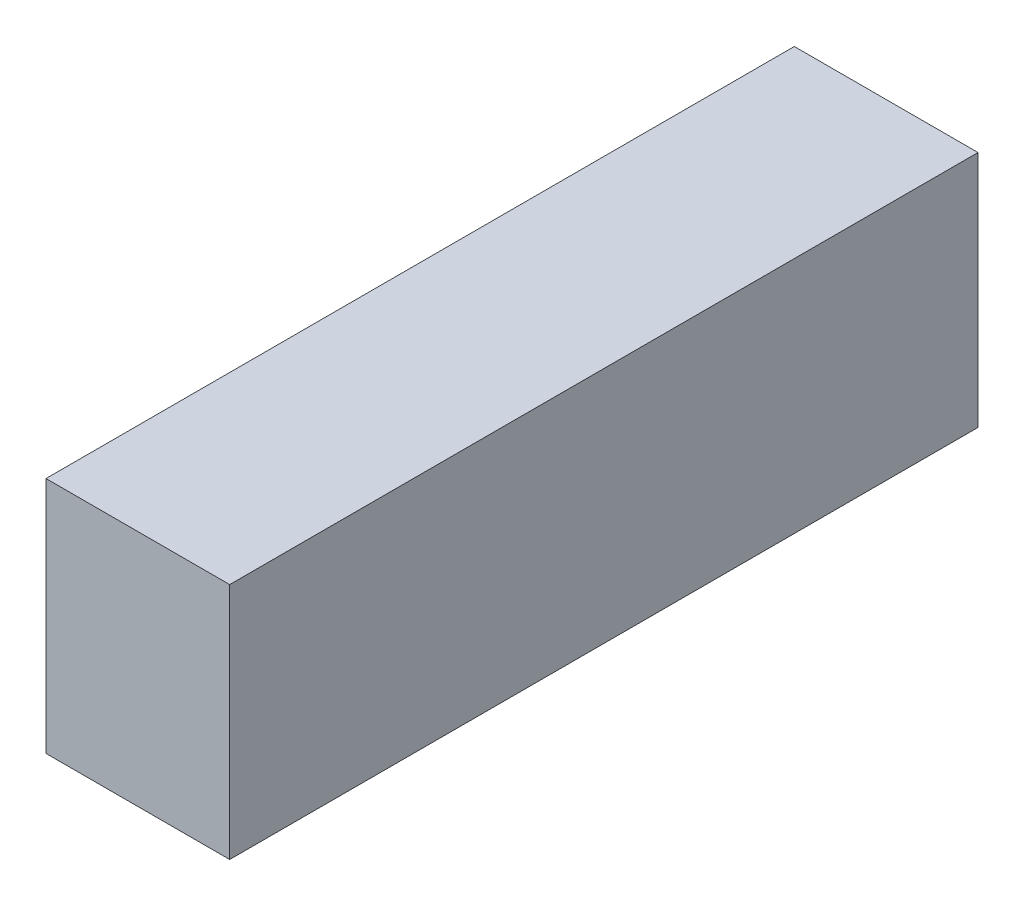
SolidWorks part; units mm, degrees
ref_plane "Front Plane" through (0, 0, 0) normal (0, 0, 1) x (1, 0, 0)
ref_plane "Top Plane" through (0, 0, 0) normal (0, 1, 0) x (1, 0, 0)
ref_plane "Right Plane" through (0, 0, 0) normal (1, 0, 0) x (0, 0, -1)
other "Bounding Box"
ref_plane "Default Plane" through (13.8565, 3.175, 6.7999) normal (0, -1, 0) x (-1, 0, 0)
sketch "Sketch1" plane through (0, 0, 0) normal (0, 1, 0) x (1, 0, 0)
  line L1 (-8.5725, -34.925) -> (8.5725, -34.925)
  line L2 (-8.5725, -34.925) -> (-8.5725, 34.925)
  line L3 (-8.5725, 34.925) -> (8.5725, 34.925)
  line L4 (8.5725, -34.925) -> (8.5725, 34.925)
  line L5 (-8.5725, -34.925) -> (8.5725, 34.925) construction
  line L6 (-8.5725, 34.925) -> (8.5725, -34.925) construction
  point P0 (0, 0)
  point P6 (7.1494, -8.5725)
  dimension "D1" = 69.85
  dimension "D2" = 17.145
extrude "Boss-Extrude1" add sketch "Sketch1" along normal mid plane 22.225
